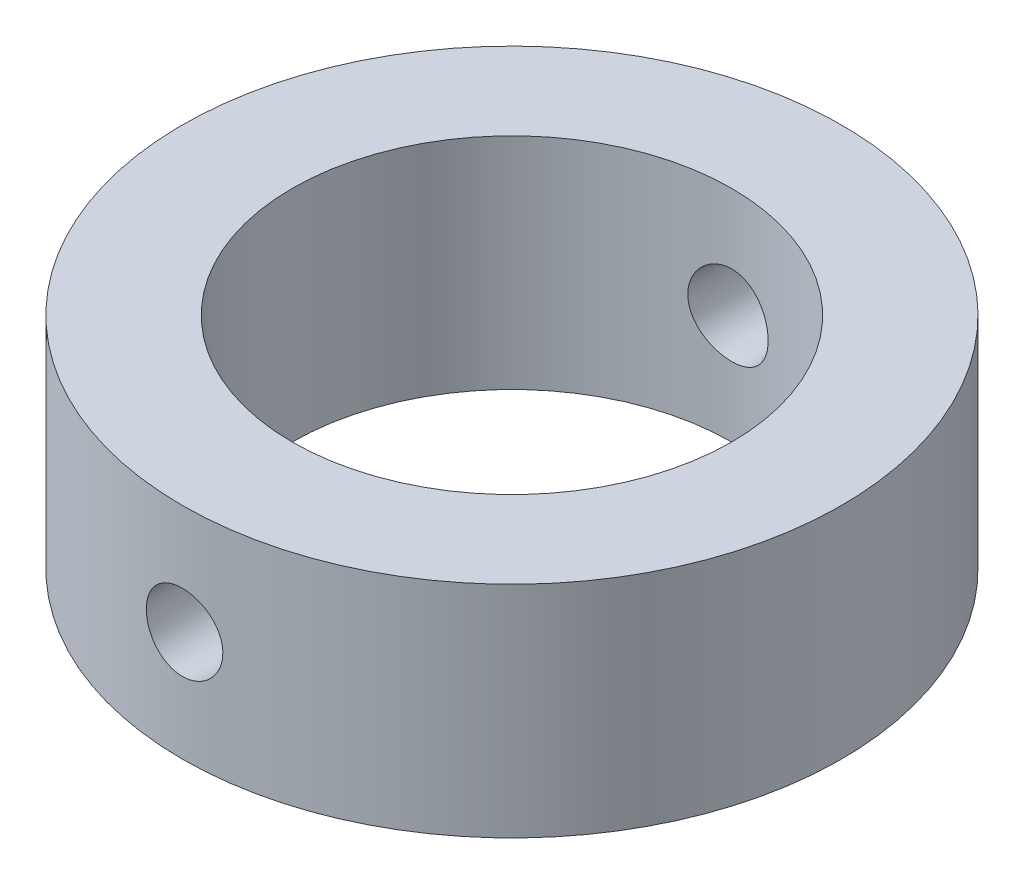
SolidWorks part; units mm, degrees
ref_plane "Front Plane" through (0, 0, 0) normal (0, 0, 1) x (1, 0, 0)
ref_plane "Top Plane" through (0, 0, 0) normal (0, 1, 0) x (1, 0, 0)
ref_plane "Right Plane" through (0, 0, 0) normal (1, 0, 0) x (0, 0, -1)
sketch "Sketch3" plane through (0, 0, 0) normal (0, 1, 0) x (1, 0, 0)
  circle A0 centre (0, 0) radius 10
  circle A1 centre (0, 0) radius 15
  dimension "D1" = 30
  dimension "D2" = 20
extrude "Boss-Extrude1" add sketch "Sketch3" along normal blind 10
sketch "Sketch4" plane through (0, 0, 0) normal (0, 0, 1) x (1, 0, 0)
  line L0 (15, 0) -> (15, 10) construction
  circle A0 centre (0, 5) radius 2
  dimension "D3" = 4
  dimension "D1" = 5
  dimension "D2" = 15
extrude "Cut-Extrude1" cut sketch "Sketch4" against normal blind 21 draft 1 and the other way blind 19 draft 1
